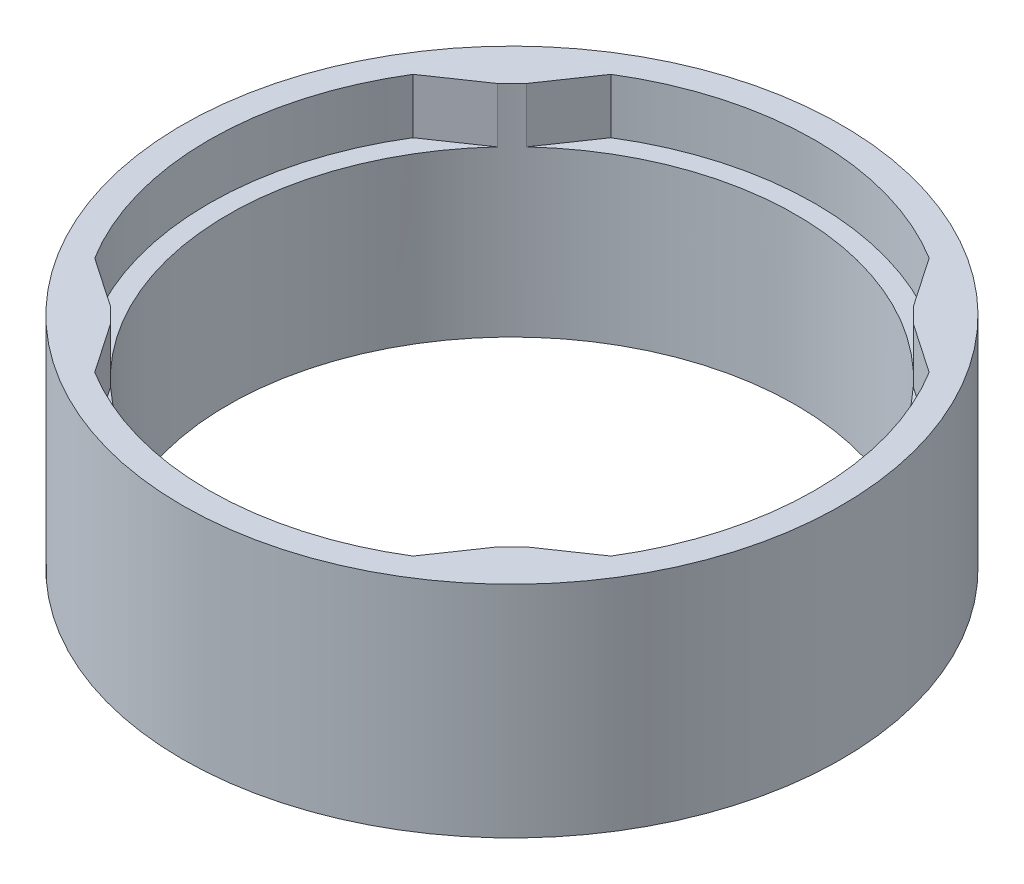
SolidWorks part; units mm, degrees
ref_plane "Front Plane" through (0, 0, 0) normal (0, 0, 1) x (1, 0, 0)
ref_plane "Top Plane" through (0, 0, 0) normal (0, 1, 0) x (1, 0, 0)
ref_plane "Right Plane" through (0, 0, 0) normal (1, 0, 0) x (0, 0, -1)
sketch "Sketch1" plane through (0, 0, 0) normal (0, 1, 0) x (1, 0, 0)
  circle A0 centre (0, 0) radius 65.659
  circle A1 centre (0, 0) radius 76.2
  dimension "D1" = 131.318
  dimension "D2" = 152.4
extrude "Boss-Extrude1" add sketch "Sketch1" against normal blind 50.8
sketch "Sketch2" plane through (0, 0, 0) normal (0, 1, 0) x (1, 0, 0)
  line L0 (-48.0809, -44.7139) -> (-59.6723, -36.7939)
  line L1 (-48.0809, 44.7139) -> (-59.6723, 36.7939)
  arc A1 (-59.6723, -36.7939) -> (-59.6723, 36.7939) centre (0, 0) cw
  arc A3 (-48.0809, -44.7139) -> (-48.0809, 44.7139) centre (0, 0) cw
  circle A4 centre (0, 0) radius 65.659 construction
  point P9 (-65.659, 0)
  point P10 (-70.104, 0)
  dimension "D1" = 70.104
  dimension "D3" = 98.3742
  dimension "D2" = 65.659
  dimension "D4" = 77.47
extrude "Cut-Extrude1" cut sketch "Sketch2" against normal blind 12.7
pattern_circular "CirPattern1" count 4 over 360 about axis through (0, 0, 0) along (0, 1, 0) of "Cut-Extrude1"
